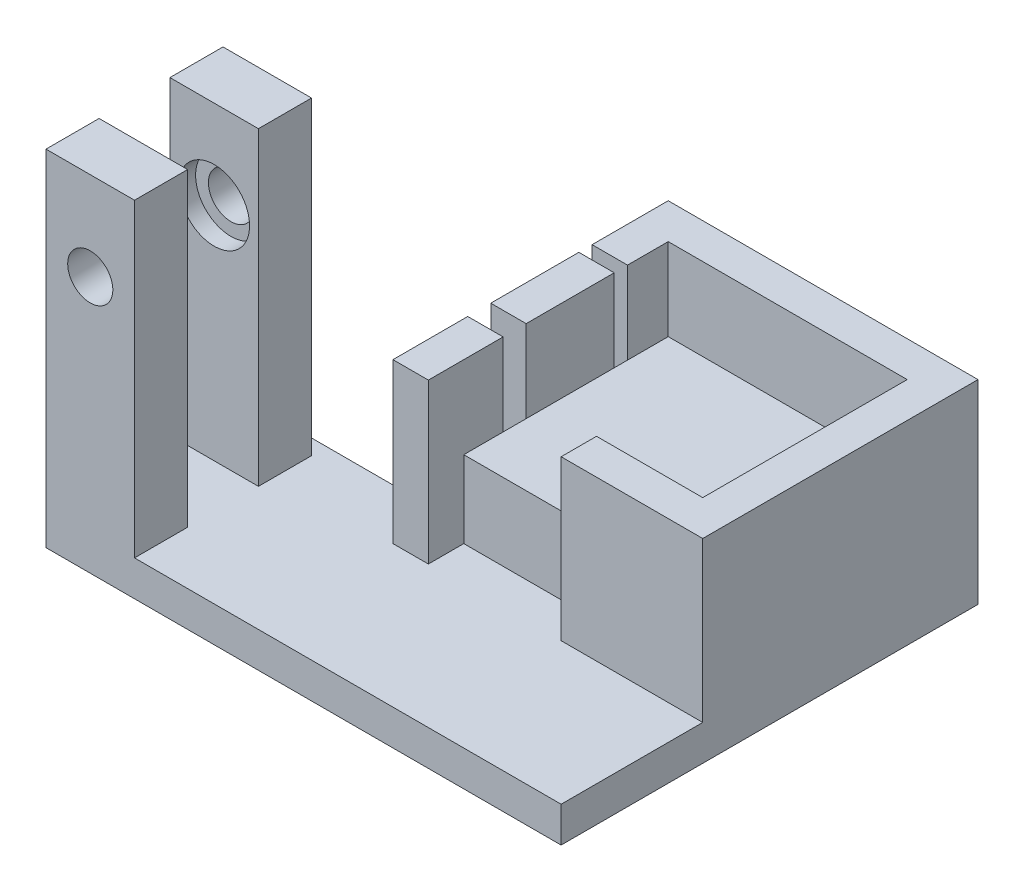
SolidWorks part; units mm, degrees
ref_plane "Front Plane" through (0, 0, 0) normal (0, 0, 1) x (1, 0, 0)
ref_plane "Top Plane" through (0, 0, 0) normal (0, 1, 0) x (1, 0, 0)
ref_plane "Right Plane" through (0, 0, 0) normal (1, 0, 0) x (0, 0, -1)
sketch "Sketch1" plane through (0, 0, 0) normal (0, 1, 0) x (1, 0, 0)
  line L1 (-27.0492, 17.9508) -> (32.9508, 17.9508)
  line L2 (-27.0492, 17.9508) -> (-27.0492, -52.0492)
  line L3 (-27.0492, -52.0492) -> (32.9508, -52.0492)
  line L4 (32.9508, 17.9508) -> (32.9508, -52.0492)
  dimension "D1" = 60
  dimension "D2" = 70
extrude "Boss-Extrude1" add sketch "Sketch1" along normal blind 4
sketch "Sketch4" plane through (0, 4, 0) normal (0, 1, 0) x (1, 0, 0)
  line L1 (1.9508, -8.9492) -> (28.9508, -8.9492)
  line L2 (1.9508, -8.9492) -> (1.9508, -32.0492)
  line L3 (1.9508, -32.0492) -> (28.9508, -32.0492)
  line L4 (28.9508, -8.9492) -> (28.9508, -32.0492)
  line L5 (-27.0492, -52.0492) -> (32.9508, -52.0492) construction
  line L6 (32.9508, -52.0492) -> (32.9508, 17.9508) construction
  dimension "D1" = 20
  dimension "D2" = 27
  dimension "D3" = 4
  dimension "D4" = 23.1
extrude "Boss-Extrude3" add sketch "Sketch4" along normal blind 8.7 contours L2 L3 L4 L1
sketch "Sketch3" plane through (0, 0, 52.0492) normal (0, 0, 1) x (1, 0, 0)
  line L0 (-25.2492, 4) -> (-25.2492, 39)
  line L1 (-25.2492, 39) -> (-15.2492, 39)
  line L2 (-15.2492, 39) -> (-15.2492, 4)
  line L3 (-27.0492, 4) -> (32.9508, 4) construction
  line L4 (-25.2492, 4) -> (-15.2492, 4)
  circle A0 centre (-20.2492, 29) radius 1.5
  dimension "D2" = 3
  dimension "D1" = 35
  dimension "D3" = 25
  dimension "D4" = 22.2
  dimension "D5" = 5
  dimension "D6" = 5
extrude "Boss-Extrude2" add sketch "Sketch3" against normal blind 6
sketch "Sketch5" plane through (0, 4, 0) normal (0, 1, 0) x (1, 0, 0)
  line L0 (1.9508, -8.9492) -> (28.9508, -8.9492) construction
  line L1 (1.9508, -8.9492) -> (1.9508, -32.0492) construction
  line L2 (1.9508, -32.0492) -> (28.9508, -32.0492) construction
  line L3 (28.9508, -8.9492) -> (28.9508, -32.0492) construction
  line L4 (1.9508, -8.9492) -> (28.9508, -8.9492)
  line L5 (1.9508, -8.9492) -> (1.9508, -32.0492)
  line L6 (1.9508, -32.0492) -> (28.9508, -32.0492)
  line L7 (28.9508, -8.9492) -> (28.9508, -32.0492)
  line L8 (-2.0492, -4.9492) -> (-2.0492, -36.0492)
  line L9 (-2.0492, -36.0492) -> (32.9508, -36.0492)
  line L10 (32.9508, -4.9492) -> (32.9508, -36.0492)
  line L11 (-2.0492, -4.9492) -> (32.9508, -4.9492)
  line L12 (16.9508, -32.0492) -> (16.9508, -36.0492)
  line L13 (1.9508, -32.0492) -> (1.9508, -36.0492)
  line L14 (28.9508, -27.5992) -> (32.9508, -27.5992)
  line L16 (28.9508, -24.9992) -> (32.9508, -24.9992)
  line L18 (15.4508, -4.9492) -> (15.4508, -36.0492) construction
  line L19 (1.9508, -27.5992) -> (-2.0492, -27.5992)
  line L20 (1.9508, -24.9992) -> (-2.0492, -24.9992)
  line L21 (1.9508, -15.0492) -> (-2.0492, -15.0492)
  line L22 (1.9508, -13.5492) -> (-2.0492, -13.5492)
  dimension "D2" = 15
  dimension "D3" = 2.6
  dimension "D4" = 4.45
  dimension "D5" = 9.95
  dimension "D6" = 1.5
  dimension "D1" = 4
extrude "Boss-Extrude4" add sketch "Sketch5" along normal blind 18
sketch "Sketch6" plane through (0, 0, 46.0492) normal (0, 0, -1) x (-1, 0, 0)
  circle A0 centre (20.2492, 29) radius 2.55
  dimension "D1" = 5.1
extrude "Cut-Extrude1" cut sketch "Sketch6" against normal up to next (6 mm away)
sketch "Sketch7" plane through (0, 0, 46.0492) normal (0, 0, -1) x (-1, 0, 0)
  circle A0 centre (20.2492, 29) radius 4
  dimension "D1" = 8
extrude "Cut-Extrude2" cut sketch "Sketch7" against normal blind 1.9
sketch "Sketch8" plane through (0, 4, 0) normal (0, 1, 0) x (1, 0, 0)
  line L0 (-27.0492, -42.0492) -> (-9.5762, -42.0492) construction
  line L1 (-27.0492, 17.9508) -> (-27.0492, -52.0492) construction
  line L2 (-25.2492, -46.0492) -> (-15.2492, -46.0492) construction
  dimension "D1" = 4
ref_plane "Plane1" through (0, 0, 42.0492) normal (0, 0, -1) x (-1, 0, 0)
mirror "Mirror1" about plane through (0, 0, 42.0492) normal (0, 0, -1) of "Cut-Extrude2", "Cut-Extrude1", "Boss-Extrude2"
sketch "Sketch9" plane through (0, 4, 0) normal (0, 1, 0) x (1, 0, 0)
  line L0 (-2.0492, -27.5992) -> (-2.0492, -36.0492) construction
  line L1 (32.9508, -4.9492) -> (-27.0492, -4.9492)
  line L2 (32.9508, -4.9492) -> (32.9508, 17.9508)
  line L3 (32.9508, 17.9508) -> (-27.0492, 17.9508)
  line L4 (-27.0492, -4.9492) -> (-27.0492, 17.9508)
  line L5 (-27.0492, -4.9492) -> (-2.0492, -4.9492)
  line L6 (-27.0492, -4.9492) -> (-27.0492, -30.3119)
  line L7 (-27.0492, -30.3119) -> (-2.0492, -30.3119)
  line L8 (-2.0492, -4.9492) -> (-2.0492, -30.3119)
  line L10 (-25.2492, -52.0492) -> (-27.0492, -52.0492)
  line L11 (-25.2492, -52.0492) -> (-25.2492, -30.3119)
  line L12 (-25.2492, -30.3119) -> (-27.0492, -30.3119)
  line L13 (-27.0492, -52.0492) -> (-27.0492, -30.3119)
  line M6 (-2.0492, -36.0492) -> (-2.0492, -27.5992)
  line M10 (-2.0492, -24.9992) -> (-2.0492, -15.0492)
  line M14 (-2.0492, -13.5492) -> (-2.0492, -4.9492)
  line M15 (-2.0492, -4.9492) -> (32.9508, -4.9492)
  line M16 (32.9508, -4.9492) -> (32.9508, 17.9508)
  line M17 (32.9508, 17.9508) -> (-27.0492, 17.9508)
  line M18 (-27.0492, 17.9508) -> (-27.0492, -52.0492)
  line M19 (-27.0492, -52.0492) -> (-25.2492, -52.0492)
  line M20 (-25.2492, -52.0492) -> (-25.2492, -46.0492)
  line M28 (-25.2492, -38.0492) -> (-25.2492, -32.0492)
extrude "Cut-Extrude3" cut sketch "Sketch9" against normal up to next contours L8 L1 L7 M14 M18 M6 M10 | L1 M15 M16 M17 M18 | L11 L7 M20 M28 M18 M19
